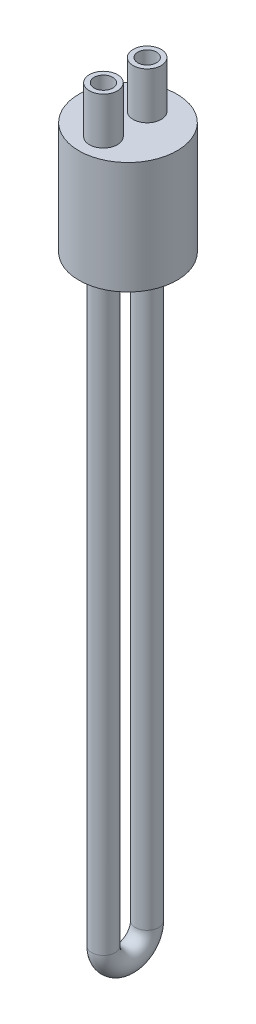
SolidWorks part; units mm, degrees
material "1060-O (SS)"
ref_plane "Front Plane" through (0, 0, 0) normal (0, 0, 1) x (1, 0, 0)
ref_plane "Top Plane" through (0, 0, 0) normal (0, 1, 0) x (1, 0, 0)
ref_plane "Right Plane" through (0, 0, 0) normal (1, 0, 0) x (0, 0, -1)
sketch "Sketch1" plane through (0, 0, 0) normal (0, 1, 0) x (1, 0, 0)
  circle A0 centre (0, 0) radius 21
  circle A1 centre (0, -10.4958) radius 4
  circle A2 centre (0, 8.2178) radius 4
  dimension "D1" = 42
  dimension "D2" = 8
  dimension "D3" = 8
extrude "Boss-Extrude1" add sketch "Sketch1" along normal blind 48
sketch "Sketch2" plane through (0, 0, 0) normal (0, -1, 0) x (1, 0, 0)
  circle A0 centre (0, 0) radius 19
  dimension "D1" = 38
extrude "Cut-Extrude1" cut sketch "Sketch2" against normal blind 42
sketch "Sketch3" plane through (0, 48, 0) normal (0, 1, 0) x (1, 0, 0)
  circle A0 centre (0, -10.4958) radius 4 construction
  circle A1 centre (0, 0) radius 21
  circle A2 centre (0, 0) radius 21
  circle A3 centre (0, 8.2178) radius 4 construction
  circle A4 centre (0, -10.4958) radius 4
  circle A5 centre (0, 8.2178) radius 4
  circle A6 centre (0, 8.2178) radius 6
  circle A7 centre (0, -10.4958) radius 6
  circle M2 centre (0, -10.4958) radius 4
  circle M4 centre (0, 8.2178) radius 4
  dimension "D1" = 0
extrude "Boss-Extrude2" add sketch "Sketch3" along normal blind 20 contours A6 M4 | A7 M2 | A4
sketch "Sketch4" plane through (0, 0, 0) normal (1, 0, 0) x (0, 0, -1)
  line L0 (8.1609, 48) -> (8.1609, -252)
  line L1 (21, 48) -> (-21, 48) construction
  line L2 (-10.4958, 48) -> (-10.4958, -252)
  line L3 (-4.4958, 48) -> (-16.4958, 48) construction
  arc A0 (-10.4958, -252) -> (8.1609, -252) centre (-1.1675, -252) ccw
  dimension "D1" = 300
sketch "Sketch7" plane through (0, 42, 0) normal (0, -1, 0) x (1, 0, 0)
  circle A0 centre (0, 10.4958) radius 4 construction
  circle A1 centre (0, 10.4958) radius 4
  circle A2 centre (0, 10.4958) radius 5
  dimension "D1" = 1
sweep "Sweep9" add profiles "Sketch7" path "Sketch4"
